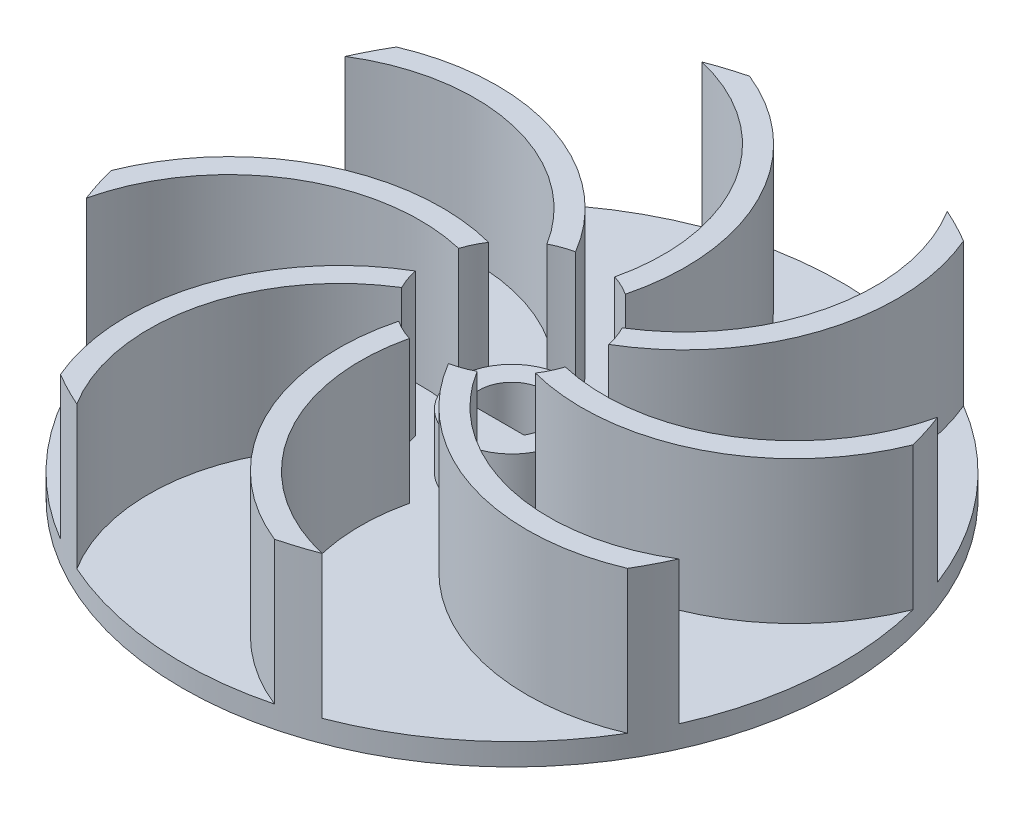
SolidWorks part; units mm, degrees
ref_plane "Front Plane" through (0, 0, 0) normal (0, 0, 1) x (1, 0, 0)
ref_plane "Top Plane" through (0, 0, 0) normal (0, 1, 0) x (1, 0, 0)
ref_plane "Right Plane" through (0, 0, 0) normal (1, 0, 0) x (0, 0, -1)
sketch "Sketch1" plane through (0, 0, 0) normal (0, 1, 0) x (1, 0, 0)
  circle A0 centre (0, 0) radius 30
  dimension "D1" = 60
extrude "Boss-Extrude1" add sketch "Sketch1" along normal blind 2
sketch "Sketch2" plane through (0, 0, 0) normal (0, 1, 0) x (1, 0, 0)
  circle A0 centre (0, 0) radius 5
  dimension "D1" = 10
extrude "Boss-Extrude2" add sketch "Sketch2" along normal blind 7
sketch "Sketch3" plane through (0, 2, 0) normal (0, 1, 0) x (1, 0, 0)
  circle A0 centre (0, 0) radius 7.4461
  circle A1 centre (0, 0) radius 30
  arc A2 (0, 0) -> (-34.3356, 6.2987) centre (-18.2133, -2.5499) ccw
  arc A3 (0.9903, 0.1386) -> (-35.2122, 6.7798) centre (-18.2133, -2.5499) ccw
  arc A4 (-0.9903, -0.1386) -> (-33.4589, 5.8175) centre (-18.2133, -2.5499) ccw
  circle M2 centre (0, 0) radius 5
  circle M3 centre (0, 0) radius 30
  dimension "D1" = 1
  dimension "D2" = 1
extrude "Boss-Extrude3" add sketch "Sketch3" along normal blind 13 contours A4 A2 M2 M3 | A3 A1 A2 M2
sketch "Sketch4" plane through (0, 0, 0) normal (0, 1, 0) x (1, 0, 0)
  line L0 (-2.5981, -1.5) -> (2.5981, -1.5)
  arc A0 (2.5981, -1.5) -> (-2.5981, -1.5) centre (0, 0) ccw
  dimension "D1" = 6
  dimension "D2" = 1.5
extrude "Cut-Extrude1" cut sketch "Sketch4" along normal through all
pattern_circular "CirPattern2" count 8 over 360 about axis through (0, 0, 0) along (0, 1, 0) of "Boss-Extrude3"
